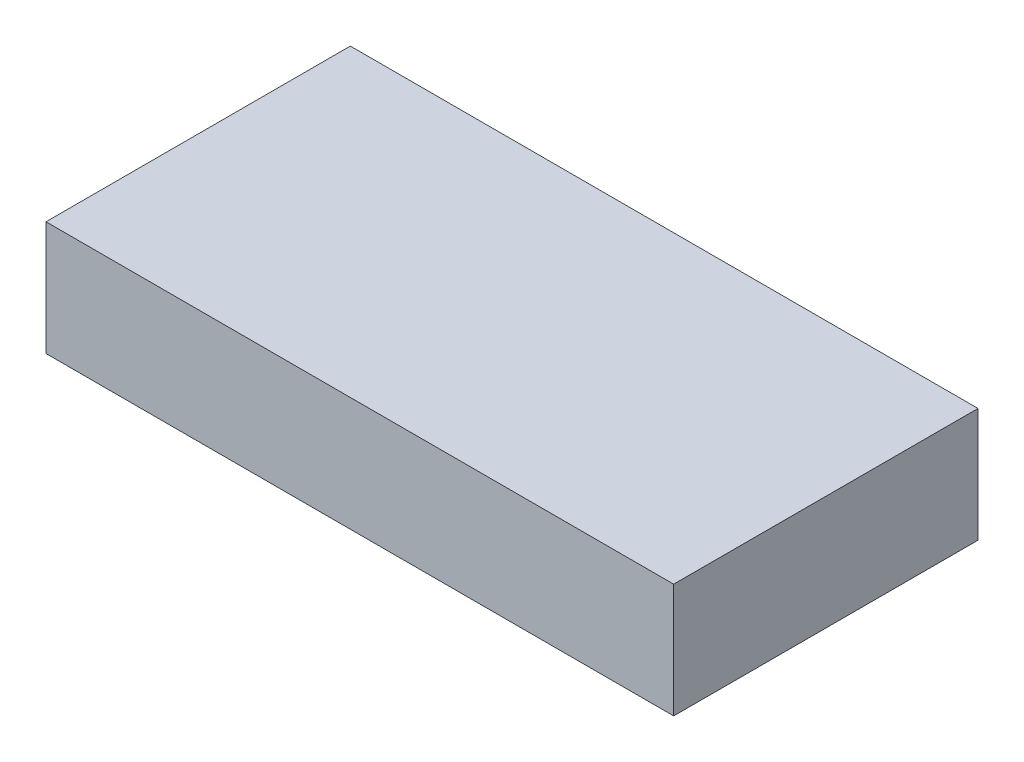
SolidWorks part; units mm, degrees
ref_plane "Front Plane" through (0, 0, 0) normal (0, 0, 1) x (1, 0, 0)
ref_plane "Top Plane" through (0, 0, 0) normal (0, 1, 0) x (1, 0, 0)
ref_plane "Right Plane" through (0, 0, 0) normal (1, 0, 0) x (0, 0, -1)
sketch "Sketch1" plane through (0, 0, 0) normal (0, 1, 0) x (1, 0, 0)
  line L1 (-16.5, 8) -> (16.5, 8)
  line L2 (-16.5, 8) -> (-16.5, -8)
  line L3 (-16.5, -8) -> (16.5, -8)
  line L4 (16.5, 8) -> (16.5, -8)
  line L5 (-16.5, 8) -> (16.5, -8) construction
  line L6 (-16.5, -8) -> (16.5, 8) construction
  point P0 (0, 0)
  dimension "D1" = 33
  dimension "D2" = 16
extrude "Boss-Extrude1" add sketch "Sketch1" along normal blind 6
